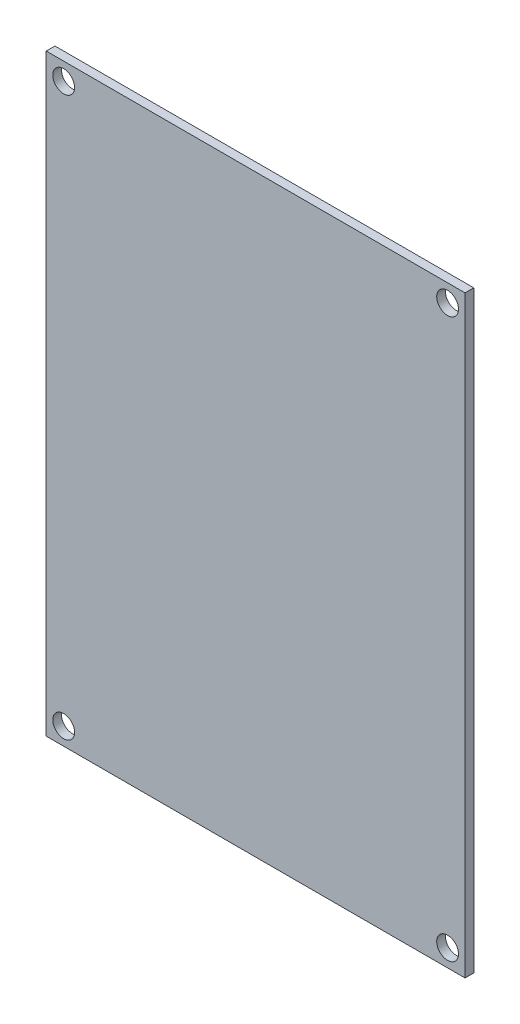
SolidWorks part; units mm, degrees
ref_plane "Plan de face" through (0, 0, 0) normal (0, 0, 1) x (1, 0, 0)
ref_plane "Plan de dessus" through (0, 0, 0) normal (0, 1, 0) x (1, 0, 0)
ref_plane "Plan de droite" through (0, 0, 0) normal (1, 0, 0) x (0, 0, -1)
sketch "Esquisse1" plane through (0, 0, 0) normal (0, 0, 1) x (1, 0, 0)
  line L1 (-290, 340) -> (190, 340)
  line L2 (-290, 340) -> (-290, -340)
  line L3 (-290, -340) -> (190, -340)
  line L4 (190, 340) -> (190, -340)
  dimension "D1" = 480
  dimension "D2" = 680
  dimension "D3" = 340
  dimension "D4" = 190
extrude "Boss.-Extru.1" add sketch "Esquisse1" along normal blind 10
sketch "Esquisse2" plane through (0, 0, 10) normal (0, 0, 1) x (1, 0, 0)
  line L0 (190, -340) -> (190, 340) construction
  line L1 (190, 340) -> (-290, 340) construction
  line L2 (-290, 340) -> (-290, -340) construction
  line L3 (-290, -340) -> (190, -340) construction
  circle A0 centre (170, 320) radius 12.5
  circle A1 centre (-270, 320) radius 12.5
  circle A2 centre (-270, -320) radius 12.5
  circle A3 centre (170, -320) radius 12.5
  dimension "D1" = 25
  dimension "D2" = 20
  dimension "D3" = 20
  dimension "D4" = 25
  dimension "D5" = 25
  dimension "D6" = 25
  dimension "D7" = 20
  dimension "D8" = 20
  dimension "D9" = 20
  dimension "D10" = 20
  dimension "D11" = 20
  dimension "D12" = 20
extrude "Enlèv. mat.-Extru.1" cut sketch "Esquisse2" against normal blind 10
